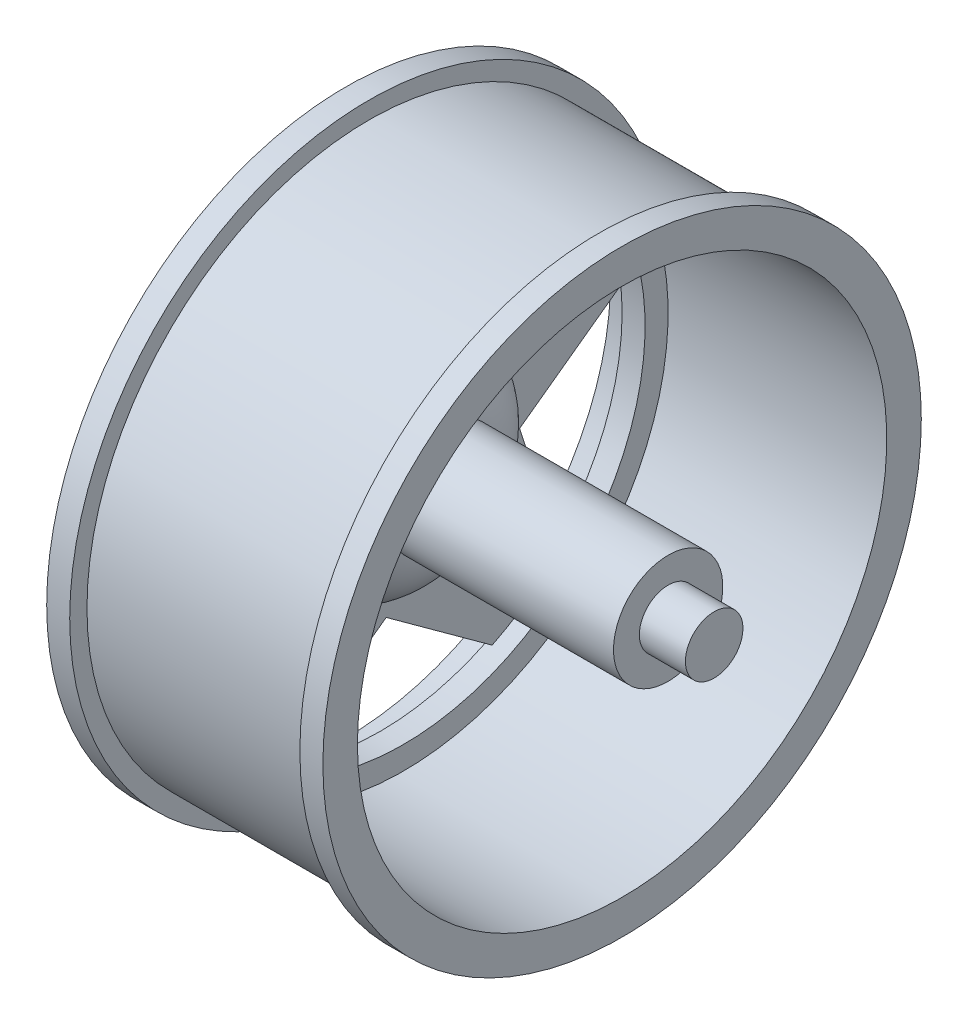
SolidWorks part; units mm, degrees
ref_plane "Plano frontal" through (0, 0, 0) normal (0, 0, 1) x (1, 0, 0)
ref_plane "Plano superior" through (0, 0, 0) normal (0, 1, 0) x (1, 0, 0)
ref_plane "Plano direito" through (0, 0, 0) normal (1, 0, 0) x (0, 0, -1)
sketch "Esboço1" plane through (0, 0, 0) normal (0, 0, 1) x (1, 0, 0)
  line L0 (0, 0) -> (23.6267, 0) construction
  line L1 (0, 26) -> (0, 23)
  line L2 (0, 23) -> (24, 23) construction
  line L3 (24, 23) -> (24, 26)
  line L4 (24, 26) -> (22, 26)
  line L5 (22, 26) -> (22, 24.5)
  line L6 (22, 24.5) -> (2, 24.5)
  line L7 (2, 24.5) -> (2, 26)
  line L8 (2, 26) -> (0, 26)
  line L9 (3, 23) -> (3, 21)
  line L10 (3, 21) -> (5, 21)
  line L11 (5, 21) -> (5, 23)
  line L12 (0, 23) -> (3, 23)
  line L13 (5, 23) -> (24, 23)
  dimension "D1" = 24
  dimension "D2" = 3
  dimension "D3" = 1.5
  dimension "D4" = 2
  dimension "D5" = 2
  dimension "D6" = 2
  dimension "D7" = 3
  dimension "D8" = 26
revolve "Revolução1" add sketch "Esboço1" angle 360 about L0
ref_plane "Plano1" through (1.5, 0, 0) normal (1, 0, 0) x (0, 0, -1)
sketch "Esboço2" plane through (1.5, 0, 0) normal (1, 0, 0) x (0, 0, -1)
  line L0 (0, 23) -> (0, 0) construction
  line L1 (0, 23) -> (-21.8743, 7.1074) construction
  line L2 (-21.8743, 7.1074) -> (-13.5191, -18.6074) construction
  line L3 (-13.5191, -18.6074) -> (13.5191, -18.6074) construction
  line L4 (13.5191, -18.6074) -> (21.8743, 7.1074) construction
  line L5 (21.8743, 7.1074) -> (0, 23) construction
  line L6 (0, 23) -> (13.5191, -18.6074) construction
  line L7 (13.5191, -18.6074) -> (-21.8743, 7.1074) construction
  line L8 (-21.8743, 7.1074) -> (21.8743, 7.1074) construction
  line L9 (21.8743, 7.1074) -> (-13.5191, -18.6074) construction
  line L10 (-13.5191, -18.6074) -> (0, 23) construction
  line L11 (2.9534, 22.8096) -> (7.1618, 9.8574)
  line L12 (-15.7965, -16.7174) -> (-11.5881, -3.7652)
  line L13 (11.0178, -20.1893) -> (0, -12.1844)
  line L14 (-20.7806, 9.8574) -> (-7.1618, 9.8574)
  line L15 (22.6059, 4.2397) -> (11.5881, -3.7652)
  line L16 (0, -12.1844) -> (-11.0178, -20.1893)
  line L17 (-11.5881, -3.7652) -> (-22.6059, 4.2397)
  line L18 (23.4907, 4.8826) -> (-11.9027, -20.8322) construction
  line L19 (-7.1618, 9.8574) -> (-2.9534, 22.8096)
  line L20 (11.9027, -20.8322) -> (-23.4907, 4.8826) construction
  line L21 (7.1618, 9.8574) -> (20.7806, 9.8574)
  line L22 (-16.1345, -17.7576) -> (-2.6154, 23.8498) construction
  line L23 (11.5881, -3.7652) -> (15.7965, -16.7174)
  line L24 (-21.8743, 9.8574) -> (21.8743, 9.8574) construction
  line L26 (2.6154, 23.8498) -> (16.1345, -17.7576) construction
  circle A0 centre (0, 0) radius 23 construction
  circle A1 centre (0, 0) radius 23 construction
  circle A2 centre (0, 0) radius 23 construction
  arc A3 (2.9534, 22.8096) -> (-2.9534, 22.8096) centre (0, 0) ccw
  arc A4 (-20.7806, 9.8574) -> (-22.6059, 4.2397) centre (0, 0) ccw
  arc A5 (-15.7965, -16.7174) -> (-11.0178, -20.1893) centre (0, 0) ccw
  arc A6 (11.0178, -20.1893) -> (15.7965, -16.7174) centre (0, 0) ccw
  arc A7 (20.7806, 9.8574) -> (22.6059, 4.2397) centre (0, 0) cw
  point P33 (0, 0)
  dimension "D1" = 2.75
  dimension "D2" = 2.75
  dimension "D3" = 2.75
  dimension "D4" = 2.75
  dimension "D5" = 2.75
extrude "Ressalto-extrusão1" add sketch "Esboço2" along normal blind 2
sketch "Esboço4" plane through (0, 0, 0) normal (0, 0, 1) x (1, 0, 0)
  line L0 (35.3696, 0) -> (43.2317, 0) construction
  line L1 (28, 4.75) -> (8.5, 4.75)
  line L2 (24, -26) -> (24, 26) construction
  line L3 (28, 4.75) -> (28, 2.5)
  line L4 (28, 2.5) -> (32, 2.5)
  line L5 (32, 2.5) -> (32, 0)
  line L6 (32, 0) -> (2.5, 0)
  line L7 (2.5, 10) -> (-7.6119, 10) construction
  line L9 (8.5, 4.75) -> (8.9258, 1.5711) construction
  line L12 (2.5, 10) -> (2.5, 0)
  line L13 (1.5, 22.8096) -> (1.5, 9.8574) construction
  arc A0 (2.5, 10) -> (8.5, 4.75) centre (2.5, 3.9464) cw
  point P4 (0, 0)
  point P13 (2.3697, 10)
  dimension "D1" = 4
  dimension "D2" = 4.75
  dimension "D3" = 2.5
  dimension "D4" = 4
  dimension "D5" = 10
  dimension "D6" = 6
  dimension "D7" = 1
revolve "Revolução2" add sketch "Esboço4" angle 360 about L0
sketch "Esboço3" plane through (0, 0, 0) normal (0, 0, 1) x (1, 0, 0)
  line L0 (0, 0) -> (-17.2258, 0) construction
  line L1 (1.5, 19.9148) -> (1.5, 21.2124) construction
  line L2 (1.5, 21.2124) -> (1.5, 23)
  line L3 (1.5, 23) -> (3, 23)
  line L4 (3, 23) -> (5.0908, 23.3687) construction
  line L5 (4.5, 4.75) -> (4.5, 0)
  line L6 (1.5, 23) -> (0, 23) construction
  line L7 (1.5, 22.8096) -> (1.5, 9.8574) construction
  line L8 (1.5, 9) -> (1.5, 0)
  line L12 (1.5, 9) -> (-16.0595, 9) construction
  line L13 (6.5, 6.9289) -> (10.4176, 3.0113) construction
  line L14 (6.5, 6.9289) -> (6.5, 4.75)
  line L15 (6.5, 4.75) -> (4.5, 4.75)
  line L16 (1.5, 0) -> (4.5, 0)
  arc A0 (1.5, 21.2124) -> (3, 23) centre (3.3152, 21.2124) cw
  arc A1 (1.5, 9) -> (6.5, 6.9289) centre (1.5, 1.9289) cw
  dimension "D1" = 10
  dimension "D2" = 1.5
  dimension "D3" = 9
  dimension "D4" = 45
  dimension "D5" = 4.75
  dimension "D6" = 5
  dimension "D7" = 2
  dimension "D8" = 2.1789
revolve "Corte-Revolução1" cut sketch "Esboço3" angle 360 about L0
